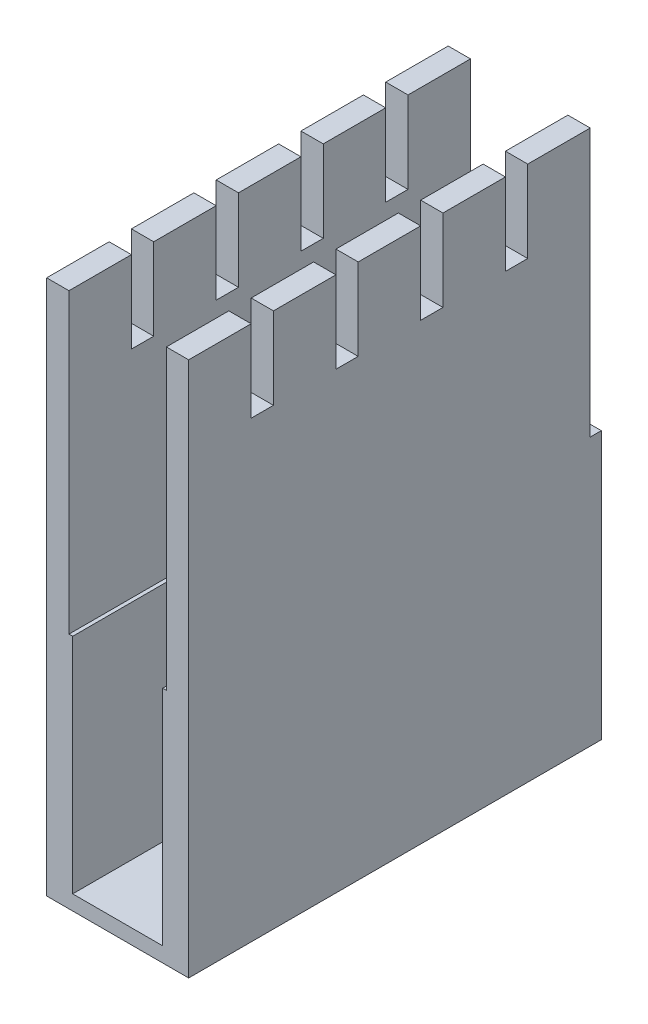
SolidWorks part; units mm, degrees
ref_plane "Front Plane" through (0, 0, 0) normal (0, 0, 1) x (1, 0, 0)
ref_plane "Top Plane" through (0, 0, 0) normal (0, 1, 0) x (1, 0, 0)
ref_plane "Right Plane" through (0, 0, 0) normal (1, 0, 0) x (0, 0, -1)
sketch "Sketch1" plane through (0, 0, 0) normal (0, 0, 1) x (1, 0, 0)
  line L0 (-9.55, 72) -> (-9.55, 0)
  line L1 (-9.55, 0) -> (9.55, 0)
  line L2 (9.55, 0) -> (9.55, 72)
  line L3 (9.55, 72) -> (6.55, 72)
  line L11 (-6.55, 72) -> (-9.55, 72)
  line L12 (-6.55, 72) -> (-6.55, 32)
  line L13 (-6.55, 32) -> (-6.05, 32)
  line L14 (-6.05, 32) -> (-6.05, 2)
  line L15 (6.55, 72) -> (6.55, 32)
  line L16 (6.55, 32) -> (6.05, 32)
  line L17 (6.05, 32) -> (6.05, 2)
  line L18 (-6.05, 2) -> (6.05, 2)
  point P11 (0, 0)
  point P25 (-8.05, 72)
  dimension "D1" = 2
  dimension "D2" = 3
  dimension "D4" = 13.1
  dimension "D5" = 12.1
  dimension "D6" = 30
  dimension "D8" = 70
extrude "Boss-Extrude1" add sketch "Sketch1" along normal blind 54
sketch "Sketch2" plane through (9.55, 0, 0) normal (1, 0, 0) x (0, 0, -1)
  line L0 (-54, 72) -> (0, 72) construction
  line L1 (-45.6, 72) -> (-42.6, 72)
  line L2 (-45.6, 72) -> (-45.6, 61)
  line L3 (-45.6, 61) -> (-42.6, 61)
  line L4 (-42.6, 72) -> (-42.6, 61)
  line L5 (-54, 66.5) -> (-45.6, 66.5) construction
  line L6 (-34.2, 72) -> (-31.2, 72)
  line L7 (-34.2, 72) -> (-34.2, 61)
  line L8 (-34.2, 61) -> (-31.2, 61)
  line L9 (-31.2, 72) -> (-31.2, 61)
  line L10 (-22.8, 72) -> (-19.8, 72)
  line L11 (-22.8, 72) -> (-22.8, 61)
  line L12 (-22.8, 61) -> (-19.8, 61)
  line L13 (-19.8, 72) -> (-19.8, 61)
  line L14 (-11.4, 72) -> (-8.4, 72)
  line L15 (-11.4, 72) -> (-11.4, 61)
  line L16 (-11.4, 61) -> (-8.4, 61)
  line L17 (-8.4, 72) -> (-8.4, 61)
  line L18 (-54, 0) -> (-54, 72) construction
  line L19 (-42.6, 66.5) -> (-34.2, 66.5) construction
  line L20 (-31.2, 66.5) -> (-22.8, 66.5) construction
  line L21 (-19.8, 66.5) -> (-11.4, 66.5) construction
  line L22 (-8.4, 66.5) -> (0, 66.5) construction
  line L23 (0, 0) -> (0, 72) construction
  dimension "D1" = 3
  dimension "D2" = 59
extrude "Cut-Extrude1" cut sketch "Sketch2" against normal through all
sketch "Sketch3" plane through (0, 0, 0) normal (0, 0, -1) x (-1, 0, 0)
  line L0 (9.55, 72) -> (9.55, 0) construction
  line L1 (-9.55, 0) -> (9.55, 0)
  line L2 (-9.55, 0) -> (-9.55, 36)
  line L3 (-9.55, 36) -> (9.55, 36)
  line L4 (9.55, 0) -> (9.55, 36)
  line L5 (-9.55, 0) -> (-9.55, 72) construction
  point P9 (-9.55, 36)
extrude "Boss-Extrude2" add sketch "Sketch3" along normal blind 1.5
